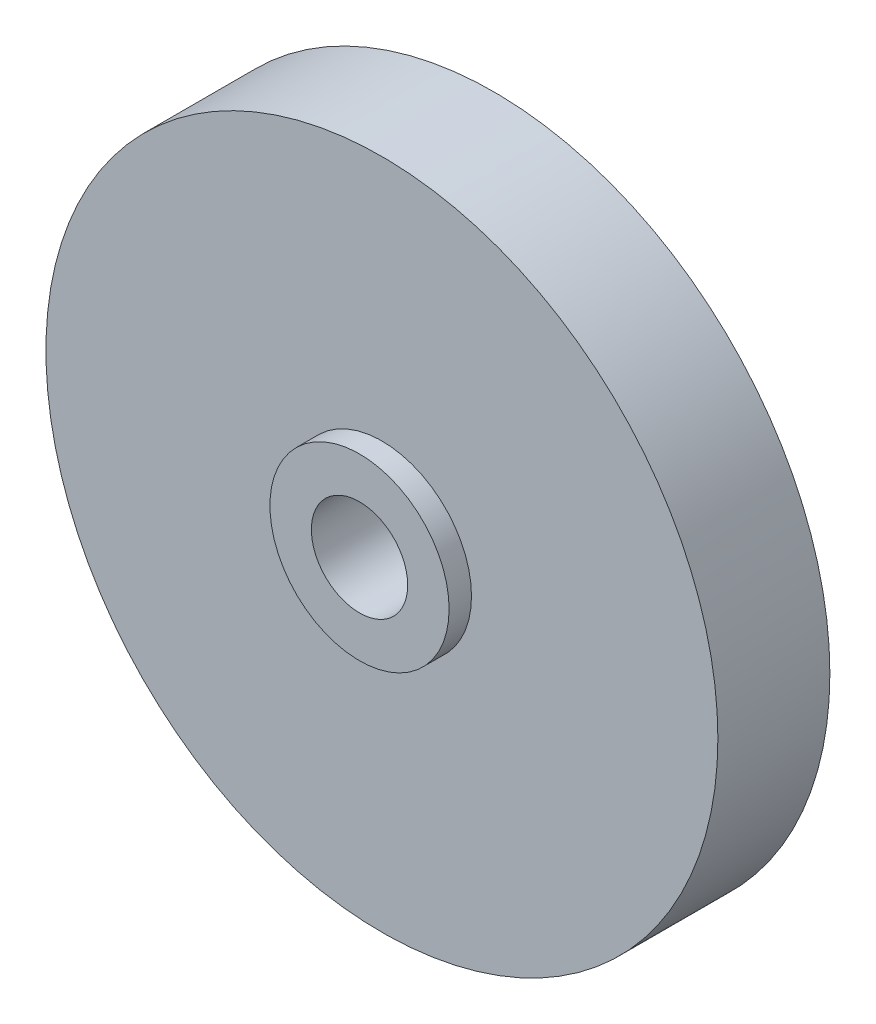
SolidWorks part; units mm, degrees
ref_plane "Front Plane" through (0, 0, 0) normal (0, 0, 1) x (1, 0, 0)
ref_plane "Top Plane" through (0, 0, 0) normal (0, 1, 0) x (1, 0, 0)
ref_plane "Right Plane" through (0, 0, 0) normal (1, 0, 0) x (0, 0, -1)
sketch "Sketch1" plane through (0, 0, 0) normal (0, 0, 1) x (1, 0, 0)
  circle A0 centre (0, 0) radius 4.3
  circle A1 centre (0, 0) radius 30
  dimension "D1" = 60
  dimension "D2" = 8.6
extrude "Boss-Extrude1" add sketch "Sketch1" along normal blind 12
sketch "Sketch2" plane through (0, 0, 0) normal (0, 0, 1) x (1, 0, 0)
  circle A0 centre (0, 0) radius 7.25
  dimension "D1" = 14.5
extrude "Cut-Extrude1" cut sketch "Sketch2" along normal blind 5
ref_plane "Plane1" through (0, 0, 12) normal (0, 0, 1) x (1, 0, 0)
sketch "Sketch3" plane through (0, 0, 12) normal (0, 0, 1) x (1, 0, 0)
  circle A0 centre (0, 0) radius 30
  circle A1 centre (0, 0) radius 8
  dimension "D1" = 16
extrude "Cut-Extrude2" cut sketch "Sketch3" against normal blind 2
